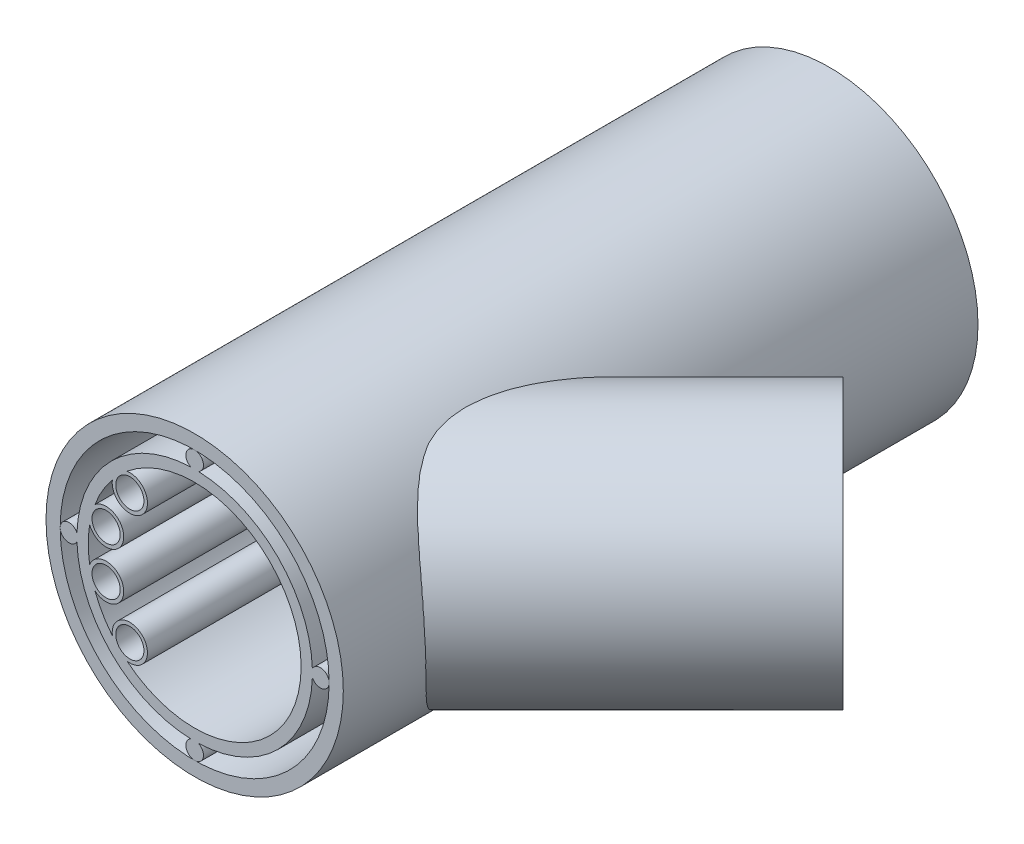
SolidWorks part; units mm, degrees
ref_plane "Front Plane" through (0, 0, 0) normal (0, 0, 1) x (1, 0, 0)
ref_plane "Top Plane" through (0, 0, 0) normal (0, 1, 0) x (1, 0, 0)
ref_plane "Right Plane" through (0, 0, 0) normal (1, 0, 0) x (0, 0, -1)
sketch "Sketch1" plane through (0, 0, 0) normal (0, 0, 1) x (1, 0, 0)
  circle A0 centre (0, 0) radius 21.08
  circle A1 centre (0, 0) radius 19.07
  dimension "D1" = 42.16
  dimension "D2" = 2.01
  dimension "D3" = 38.14
extrude "Boss-Extrude1" add sketch "Sketch1" against normal blind 90
sketch "Sketch3" plane through (0, 0, 0) normal (0, 0, 1) x (1, 0, 0)
  circle A0 centre (0, 0) radius 16.7
  circle A1 centre (0, 0) radius 15.1
  dimension "D1" = 33.4
  dimension "D2" = 1.6
extrude "Boss-Extrude2" add sketch "Sketch3" against normal blind 90 separate body
sketch "Sketch4" plane through (0, 0, 0) normal (0, 0, 1) x (1, 0, 0)
  circle A0 centre (0, -17.82) radius 1.25
  circle A6 centre (-17.82, 0) radius 1.25
  circle A7 centre (0, 17.82) radius 1.25
  circle A8 centre (17.82, 0) radius 1.25
  point P12 (0, 0)
  dimension "D1" = 4
  dimension "D4" = 2.5
  dimension "D5" = 17.82
extrude "Boss-Extrude3" add sketch "Sketch4" against normal blind 90
ref_plane "Plane1" through (0, 0, 0) normal (0.7071, 0, -0.7071) x (-0.7071, 0, -0.7071)
ref_plane "Plane2" through (45.9619, 0, -45.9619) normal (0.7071, 0, -0.7071) x (-0.7071, 0, -0.7071)
sketch "Sketch5" plane through (45.9619, 0, -45.9619) normal (0.7071, 0, -0.7071) x (-0.7071, 0, -0.7071)
  circle A0 centre (9.9856, 0.5373) radius 16.7
  circle A1 centre (9.9856, 0.5373) radius 15.1
  dimension "D1" = 33.4
  dimension "D2" = 1.6
  dimension "D3" = 10
extrude "Boss-Extrude8" add sketch "Sketch5" against normal blind 50 separate body contours A0
sketch "Sketch6" plane through (0, 0, 0) normal (0, 0, 1) x (1, 0, 0)
  circle A0 centre (0, 0) radius 15.1 construction
  circle A1 centre (0, 0) radius 15.1
extrude "Cut-Extrude1" cut sketch "Sketch6" against normal through all
sketch "Sketch7" plane through (-82.0711, 0, -173.9949) normal (-0.7071, 0, 0.7071) x (0.7071, 0, 0.7071)
  circle A0 centre (171.0805, 0.5373) radius 15.1 construction
  circle A1 centre (171.0805, 0.5373) radius 15.1
sketch "Sketch8" plane through (0, 0, 0) normal (0, 0, 1) x (1, 0, 0)
  circle A0 centre (0, 0) radius 15.1 construction
  circle A1 centre (0, 0) radius 15.1
  circle A2 centre (-9.1924, -9.1924) radius 2.5
  circle A3 centre (-9.1924, -9.1924) radius 2
  circle A4 centre (-12.557, -3.3646) radius 2
  circle A5 centre (-12.557, -3.3646) radius 2.5
  circle A6 centre (-12.557, 3.3646) radius 2
  circle A7 centre (-12.557, 3.3646) radius 2.5
  circle A8 centre (-9.1924, 9.1924) radius 2
  circle A9 centre (-9.1924, 9.1924) radius 2.5
  point P20 (0, 0)
  dimension "D1" = 5
  dimension "D2" = 13
  dimension "D3" = 0.5
  dimension "D4" = 4
extrude "Cut-Extrude3" cut sketch "Sketch7" along normal blind 50
extrude "Boss-Extrude9" add sketch "Sketch8" against normal through all contours A5 | A4 | A3 | A2 | A6 | A7 | A8 | A9
